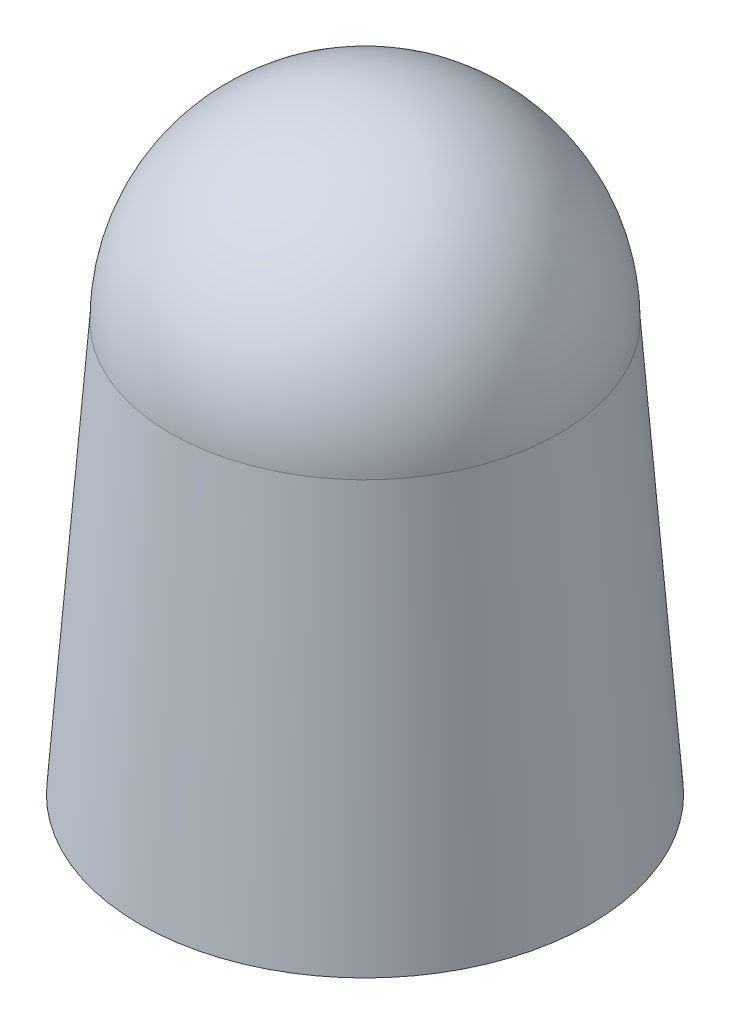
SolidWorks part; units mm, degrees
ref_plane "Front Plane" through (0, 0, 0) normal (0, 0, 1) x (1, 0, 0)
ref_plane "Top Plane" through (0, 0, 0) normal (0, 1, 0) x (1, 0, 0)
ref_plane "Right Plane" through (0, 0, 0) normal (1, 0, 0) x (0, 0, -1)
sketch "Sketch3" plane through (0, 0, 0) normal (0, 0, 1) x (1, 0, 0)
  line L0 (0, 0) -> (11, 0)
  line L1 (0, 0) -> (0, 20)
  line L2 (0, 20) -> (9.5, 20)
  line L3 (9.5, 20) -> (11, 0)
  dimension "0.6" = 9.5
  dimension "D2" = 11
  dimension "D3" = 20
revolve "Revolve1" add sketch "Sketch3" angle 360 about L1
sketch "Sketch6" plane through (0, 20, 0) normal (0, 1, 0) x (1, 0, 0)
  circle A0 centre (0, 0) radius 8.5
  circle A1 centre (0, 0) radius 9.5 construction
  dimension "D1" = 1
extrude "Cut-Extrude1" cut sketch "Sketch6" against normal blind 20
sketch "Sketch7" plane through (0, 0, 0) normal (0, 0, 1) x (1, 0, 0)
  line L4 (8.5, 19.6) -> (8.5, 0.4)
  line L6 (8.5, 0) -> (8.5, 20) construction
  line L8 (0, 0) -> (0, 24.971) construction
  line L12 (11, 0) -> (9.5, 20) construction
  line L17 (9.5, 20) -> (-9.5, 20) construction
  line L19 (8.5, 0.4) -> (10.5689, 0.4)
  line L20 (10.5689, 0.4) -> (9.1289, 19.6)
  line L21 (9.1289, 19.6) -> (8.5, 19.6)
  line L22 (-11, 0) -> (11, 0) construction
  dimension "D1" = 0.4
  dimension "D2" = 0.4
  dimension "D3" = 0.4
sketch "Sketch8" plane through (0, 0, 0) normal (0, -1, 0) x (-1, 0, 0)
  circle A0 centre (0, 0) radius 8.7076
  circle A1 centre (0, 0) radius 10.8024
revolve "Cut-Revolve1" cut sketch "Sketch7" angle 360 about L8
extrude "Cut-Extrude2" cut sketch "Sketch8" against normal blind 0.5
sketch "Sketch10" plane through (0, 20, 0) normal (0, 1, 0) x (1, 0, 0)
  line L0 (0, 9.5) -> (0, -9.5)
  circle A0 centre (0, 0) radius 9.5 construction
  arc A1 (0, 9.5) -> (0, -9.5) centre (0, 0) cw
revolve "Revolve2" add sketch "Sketch10" angle 180 about L0
